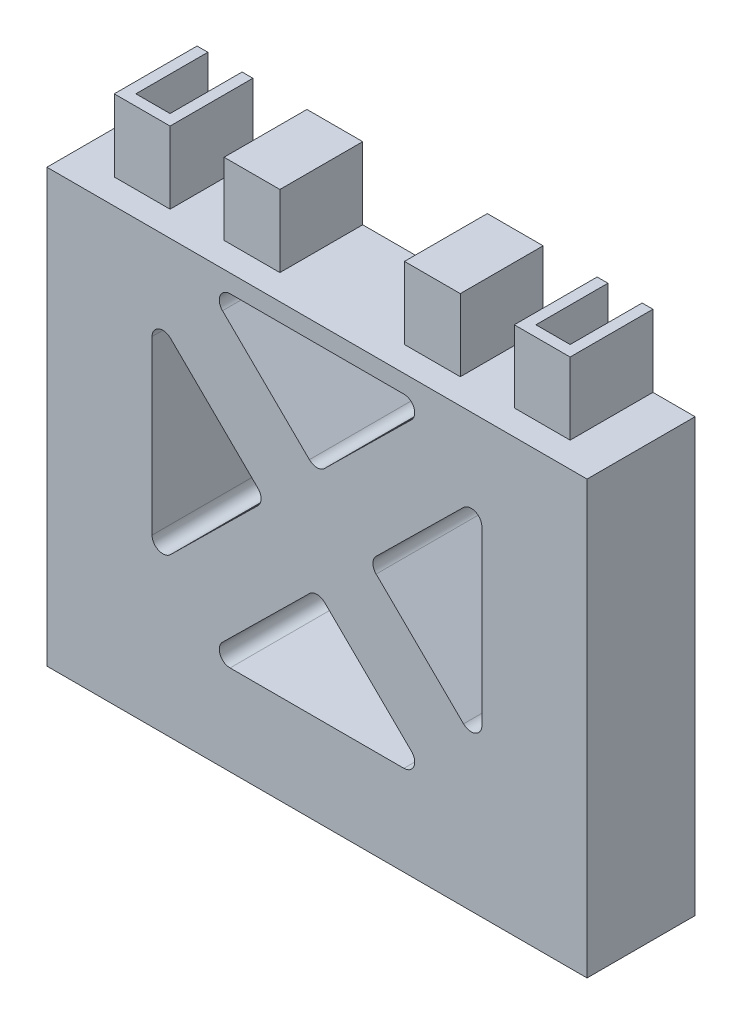
SolidWorks part; units mm, degrees
ref_plane "Front Plane" through (0, 0, 0) normal (0, 0, 1) x (1, 0, 0)
ref_plane "Top Plane" through (0, 0, 0) normal (0, 1, 0) x (1, 0, 0)
ref_plane "Right Plane" through (0, 0, 0) normal (1, 0, 0) x (0, 0, -1)
sketch "Sketch1" plane through (0, 0, 0) normal (0, 1, 0) x (1, 0, 0)
  line L0 (-50.8, 15) -> (50.8, 15) construction
  line L1 (-70, -15) -> (70, -15)
  line L2 (-70, -15) -> (-70, 15)
  line L3 (-70, 15) -> (70, 15)
  line L4 (70, -15) -> (70, 15)
  line L5 (-70, -15) -> (70, 15) construction
  line L6 (-70, 15) -> (70, -15) construction
  line L7 (-50.8, 5) -> (50.8, 5) construction
  line L8 (-50.8, 15) -> (-60.3, 15)
  line L9 (-50.8, 15) -> (-50.8, -5)
  line L10 (-50.8, -5) -> (-60.3, -5)
  line L11 (-60.3, 15) -> (-60.3, -5)
  line L12 (50.8, 15) -> (60.3, 15)
  line L13 (50.8, 15) -> (50.8, -5)
  line L14 (50.8, -5) -> (60.3, -5)
  line L15 (60.3, 15) -> (60.3, -5)
  line L17 (-41.1, -5) -> (41.1, -5)
  line L18 (-41.1, -5) -> (-41.1, 15)
  line L19 (-41.1, 15) -> (41.1, 15)
  line L20 (41.1, -5) -> (41.1, 15)
  line L21 (-41.1, -5) -> (41.1, 15) construction
  line L22 (-41.1, 15) -> (41.1, -5) construction
  point P0 (0, 0)
  point P9 (0, 15)
  point P17 (0, 5)
  dimension "D1" = 140
  dimension "D2" = 30
  dimension "D3" = 101.6
  dimension "D4" = 9.5
  dimension "D5" = 9.5
  dimension "D6" = 20
  dimension "D7" = 20
  dimension "D8" = 9.7
  dimension "D9" = 9.7
extrude "Boss-Extrude1" add sketch "Sketch1" along normal blind 120 contours L20 L17 L18 L3 L9 L10 L11 L2 L1 L4 L15 L14 L13
sketch "Sketch2" plane through (0, 120, 0) normal (0, 1, 0) x (1, 0, 0)
  line L36 (-63.3, -8) -> (-63.3, 15)
  line L37 (-47.8, -8) -> (-63.3, -8)
  line L38 (-47.8, 15) -> (-47.8, -8)
  line L39 (-63.3, -8) -> (-63.3, 15)
  line L40 (-47.8, -8) -> (-63.3, -8)
  line L41 (-47.8, 15) -> (-47.8, -8)
  line L42 (-63.3, 15) -> (-60.3, 15)
  line L43 (-60.3, 15) -> (-60.3, -5)
  line L44 (-60.3, -5) -> (-50.8, -5)
  line L45 (63.3, -8) -> (63.3, 15)
  line L46 (47.8, -8) -> (63.3, -8)
  line L47 (47.8, 15) -> (47.8, -8)
  line L48 (63.3, -8) -> (63.3, 15)
  line L49 (47.8, -8) -> (63.3, -8)
  line L50 (47.8, 15) -> (47.8, -8)
  line L51 (-50.8, -5) -> (-50.8, 15)
  line L52 (-50.8, 15) -> (-47.8, 15)
  line L53 (47.8, 15) -> (50.8, 15)
  line L54 (50.8, 15) -> (50.8, -5)
  line L55 (50.8, -5) -> (60.3, -5)
  line L56 (60.3, -5) -> (60.3, 15)
  line L57 (60.3, 15) -> (63.3, 15)
  dimension "D1" = 3
  dimension "D2" = 3
extrude "Boss-Extrude2" add sketch "Sketch2" along normal blind 20
sketch "Sketch3" plane through (0, 0, 0) normal (0, -1, 0) x (1, 0, 0)
  line L16 (-47.8, 8) -> (-47.8, -15)
  line L17 (-63.3, 8) -> (-47.8, 8)
  line L18 (-63.3, -15) -> (-63.3, 8)
  line L19 (-47.8, 8) -> (-47.8, -15)
  line L20 (-63.3, 8) -> (-47.8, 8)
  line L21 (-63.3, -15) -> (-63.3, 8)
  line L25 (-63.3, -15) -> (-60.3, -15)
  line L26 (-60.3, -15) -> (-60.3, 5)
  line L27 (-60.3, 5) -> (-50.8, 5)
  line L28 (63.3, 8) -> (63.3, -15)
  line L29 (47.8, 8) -> (63.3, 8)
  line L30 (47.8, -15) -> (47.8, 8)
  line L31 (63.3, 8) -> (63.3, -15)
  line L32 (47.8, 8) -> (63.3, 8)
  line L33 (47.8, -15) -> (47.8, 8)
  line L34 (-50.8, 5) -> (-50.8, -15)
  line L35 (-50.8, -15) -> (-47.8, -15)
  line L36 (47.8, -15) -> (50.8, -15)
  line L37 (50.8, -15) -> (50.8, 5)
  line L38 (50.8, 5) -> (60.3, 5)
  line L39 (60.3, 5) -> (60.3, -15)
  line L40 (60.3, -15) -> (63.3, -15)
  dimension "D1" = 3
  dimension "D2" = 3
extrude "Cut-Extrude1" cut sketch "Sketch3" against normal blind 20
sketch "Sketch17" plane through (0, 0, 5) normal (0, 0, -1) x (-1, 0, 0)
  line L1 (41.1, 0) -> (-41.1, 0)
  line L2 (41.1, 0) -> (41.1, 120)
  line L3 (41.1, 120) -> (-41.1, 120)
  line L4 (-41.1, 0) -> (-41.1, 120)
  line L5 (41.1, 0) -> (-41.1, 120) construction
  line L6 (41.1, 120) -> (-41.1, 0) construction
  point P0 (0, 60)
extrude "Boss-Extrude3" add sketch "Sketch17" along normal blind 20
sketch "Sketch18" plane through (0, 0, 0) normal (0, -1, 0) x (1, 0, 0)
  line L0 (-47.8, -15) -> (47.8, -15) construction
  line L1 (-32.8, -15) -> (-17.3, -15)
  line L2 (-32.8, -15) -> (-32.8, 8)
  line L3 (-32.8, 8) -> (-17.3, 8)
  line L4 (-17.3, -15) -> (-17.3, 8)
  line L5 (-47.8, -15) -> (-47.8, 8) construction
  line L6 (17.3, -15) -> (32.8, -15)
  line L7 (17.3, -15) -> (17.3, 8)
  line L8 (17.3, 8) -> (32.8, 8)
  line L9 (32.8, -15) -> (32.8, 8)
  line L10 (47.8, 8) -> (47.8, -15) construction
  dimension "D1" = 23
  dimension "D2" = 23
  dimension "D3" = 15.5
  dimension "D4" = 15.5
  dimension "D5" = 15
  dimension "D6" = 15
extrude "Cut-Extrude2" cut sketch "Sketch18" against normal blind 20
sketch "Sketch19" plane through (0, 120, 0) normal (0, 1, 0) x (1, 0, 0)
  line L0 (-47.8, 15) -> (47.8, 15) construction
  line L1 (-32.8, 15) -> (-17.3, 15)
  line L2 (-32.8, 15) -> (-32.8, -8)
  line L3 (-32.8, -8) -> (-17.3, -8)
  line L4 (-17.3, 15) -> (-17.3, -8)
  line L5 (-47.8, -8) -> (-47.8, 15) construction
  line L6 (32.8, 15) -> (17.3, 15)
  line L7 (32.8, 15) -> (32.8, -8)
  line L8 (32.8, -8) -> (17.3, -8)
  line L9 (17.3, 15) -> (17.3, -8)
  line L10 (47.8, 15) -> (47.8, -8) construction
  dimension "D1" = 23
  dimension "D2" = 23
  dimension "D3" = 15.5
  dimension "D4" = 15.5
  dimension "D5" = 15
  dimension "D6" = 15
extrude "Boss-Extrude4" add sketch "Sketch19" along normal blind 20
sketch "Sketch20" plane through (0, 0, -15) normal (0, 0, -1) x (-1, 0, 0)
  line L0 (-50.8, 120) -> (50.8, 120) construction
  line L2 (50.8, 140) -> (50.8, 20) construction
  line L3 (-50.8, 120) -> (-50.8, 20) construction
  line L4 (-50.8, 20) -> (50.8, 20) construction
  line L5 (50.8, 20) -> (50.8, 120) construction
  line L6 (50.8, 120) -> (-50.8, 20) construction
  line L7 (-50.8, 120) -> (50.8, 20) construction
  line L8 (-57.8147, 112.873) -> (43.7853, 12.873) construction
  line L9 (43.7853, 127.127) -> (-57.8147, 27.127) construction
  line L10 (-43.7853, 127.127) -> (57.8147, 27.127) construction
  line L11 (57.8147, 112.873) -> (-43.7853, 12.873) construction
  line L12 (-45.8, 115) -> (45.8, 115) construction
  line L13 (45.8, 25) -> (45.8, 115) construction
  line L14 (-45.8, 25) -> (45.8, 25) construction
  line L15 (-45.8, 115) -> (-45.8, 25) construction
  line L16 (0, 25) -> (31.4643, 25)
  line L17 (31.4643, 25) -> (0, 55.9688)
  line L18 (0, 55.9688) -> (-31.4643, 25)
  line L19 (-31.4643, 25) -> (0, 25)
  line L20 (45.8, 70) -> (45.8, 101.0475)
  line L21 (45.8, 101.0475) -> (14.2557, 70)
  line L22 (14.2557, 70) -> (45.8, 38.9525)
  line L23 (45.8, 38.9525) -> (45.8, 70)
  line L24 (0, 115) -> (-31.4643, 115)
  line L25 (-31.4643, 115) -> (0, 84.0312)
  line L26 (0, 84.0312) -> (31.4643, 115)
  line L27 (31.4643, 115) -> (0, 115)
  line L28 (-45.8, 70) -> (-45.8, 101.0475)
  line L29 (-45.8, 101.0475) -> (-14.2557, 70)
  line L30 (-14.2557, 70) -> (-45.8, 38.9525)
  line L31 (-45.8, 38.9525) -> (-45.8, 70)
  point P3 (0, 120)
  dimension "D1" = 10
  dimension "D2" = 10
  dimension "D3" = 5
extrude "Cut-Extrude3" cut sketch "Sketch20" against normal blind 37
sketch "Sketch21" plane through (70, 0, 0) normal (1, 0, 0) x (0, 0, -1)
  line L0 (15, 120) -> (5, 120) construction
  line L1 (-15, 120) -> (15, 120) construction
  line L2 (5, 120) -> (5, 20) construction
  point P6 (5, 107.5)
  point P7 (5, 95)
  point P8 (5, 82.5)
  point P9 (5, 70)
  point P10 (5, 57.5)
  point P11 (5, 45)
  point P12 (5, 32.5)
fillet "Fillet3" radius 3 12 edges at (-45.8, 38.9525, 0) (-45.8, 101.0475, 0) (-14.2557, 70, 0) (31.4643, 115, 0) (-31.4643, 115, 0) (0, 84.0312, 0) (45.8, 38.9525, 0) (45.8, 101.0475, 0) (14.2557, 70, 0) (-31.4643, 25, 0) (0, 55.9688, 0) (31.4643, 25, 0)
sketch "Sketch22" plane through (70, 0, 0) normal (1, 0, 0) x (0, 0, -1)
  line L1 (-15, 120) -> (15, 120)
  line L2 (-15, 120) -> (-15, 0)
  line L3 (-15, 0) -> (15, 0)
  line L4 (15, 120) -> (15, 0)
extrude "Boss-Extrude5" add sketch "Sketch22" along normal blind 5
sketch "Sketch23" plane through (-70, 0, 0) normal (-1, 0, 0) x (0, 0, 1)
  line L1 (-15, 120) -> (15, 120)
  line L2 (-15, 120) -> (-15, 0)
  line L3 (-15, 0) -> (15, 0)
  line L4 (15, 120) -> (15, 0)
extrude "Boss-Extrude6" add sketch "Sketch23" along normal blind 5
hole_wizard "CSK for M8 Flat Head Machine Screw1" [suppressed] positions "Sketch26" profile "Sketch25" countersink size "M8" standard "ANSI Metric"
sketch "Sketch26" [suppressed] plane through (75, 0, 0) normal (1, 0, 0) x (0, 0, -1)
  point P0 (5, 107.5)
  point P3 (5, 32.5)
sketch "Sketch25" [suppressed] plane through (75, 107.5, -5) normal (0, 1, 0) x (0, 0, -1)
  line L0 (0, 0) -> (0, 42.7039)
  line L1 (0, 42.7039) -> (4.5, 40)
  line L2 (4.5, 40) -> (4.5, 4.15)
  line L3 (4.5, 4.15) -> (8.65, 0)
  line L5 (8.65, 0) -> (0, 0)
  line L6 (-4.5, 4.15) -> (-8.65, 0) construction
  line L10 (0, 42.7039) -> (-4.5, 40) construction
  line L11 (0, -6.35) -> (0, 107.95) construction
  dimension "Hole Dia." = 9
  dimension "Hole Depth" = 40
  dimension "Near C'Sink Dia." = 17.3
  dimension "Near C'Sink Angle" = 90
  dimension "Drill Angle" = 118
hole_wizard "CSK for M8 Flat Head Machine Screw2" [suppressed] positions "Sketch27" profile "Sketch28" countersink size "M8" standard "ANSI Metric"
sketch "Sketch27" plane through (-75, 0, 0) normal (-1, 0, 0) x (0, 0, 1)
  point P0 (-5, 107.5)
  point P3 (-5, 32.5)
sketch "Sketch28" plane through (-75, 107.5, -5) normal (0, 1, 0) x (0, 0, 1)
  line L0 (0, 0) -> (0, 42.7039)
  line L1 (0, 42.7039) -> (4.5, 40)
  line L2 (4.5, 40) -> (4.5, 4.15)
  line L3 (4.5, 4.15) -> (8.65, 0)
  line L5 (8.65, 0) -> (0, 0)
  line L6 (-4.5, 4.15) -> (-8.65, 0) construction
  line L10 (0, 42.7039) -> (-4.5, 40) construction
  line L11 (0, -6.35) -> (0, 107.95) construction
  dimension "Hole Dia." = 9
  dimension "Hole Depth" = 40
  dimension "Near C'Sink Dia." = 17.3
  dimension "Near C'Sink Angle" = 90
  dimension "Drill Angle" = 118
hole_wizard "#8 Clearance Hole1" positions "3DSketch1" profile "Sketch29" hole size "#8" standard "ANSI Inch"
sketch3d "3DSketch1"
  line L0 (-75, 120, -15) -> (-75, 0, -15) construction
  line L1 (-75, 120, 15) -> (-75, 120, -15) construction
  line L2 (-75, 0, -15) -> (-75, 0, 15) construction
  point P0 (-75, 107.5, -5)
  point P2 (-75, 32.5, -5)
  dimension "D1" = 10
  dimension "D2" = 10
  dimension "D3" = 12.5
  dimension "D4" = 32.5
sketch "Sketch29" plane through (-75, 107.5, -5) normal (0, 1, 0) x (0, 0, 1)
  line L0 (0, 0) -> (0, 16.0497)
  line L1 (0, 16.0497) -> (2.2479, 14.699)
  line L2 (2.2479, 14.699) -> (2.2479, 0)
  line L5 (2.2479, 0) -> (0, 0)
  line L10 (0, 16.0497) -> (-2.2479, 14.699) construction
  line L11 (0, -6.35) -> (0, 107.95) construction
  dimension "Hole Dia." = 4.4958
  dimension "Hole Depth" = 14.699
  dimension "Drill Angle" = 118
